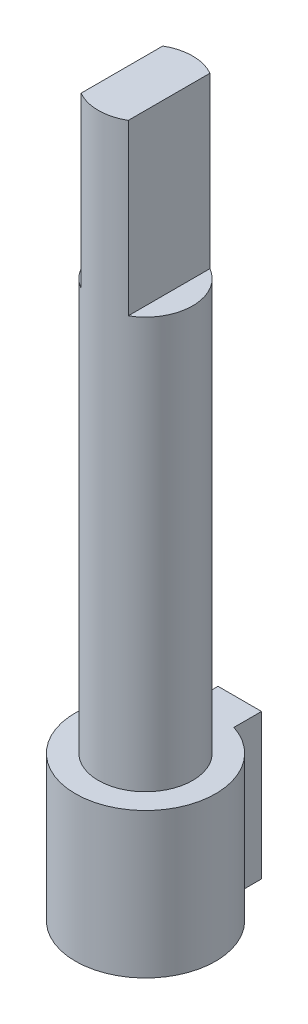
SolidWorks part; units mm, degrees
ref_plane "Front Plane" through (0, 0, 0) normal (0, 0, 1) x (1, 0, 0)
ref_plane "Top Plane" through (0, 0, 0) normal (0, 1, 0) x (1, 0, 0)
ref_plane "Right Plane" through (0, 0, 0) normal (1, 0, 0) x (0, 0, -1)
sketch "Sketch1" plane through (0, 0, 0) normal (0, 1, 0) x (1, 0, 0)
  line L1 (-1, 2.8284) -> (1, 2.8284)
  line L2 (-1, 2.8284) -> (-1, 3.9984)
  line L3 (-1, 3.9984) -> (1, 3.9984)
  line L4 (1, 2.8284) -> (1, 3.9984)
  circle A0 centre (0, 0) radius 3
  point P7 (0, 0)
  point P8 (0, 2.8284)
  dimension "D1" = 6
  dimension "D2" = 1.17
  dimension "D3" = 2
extrude "Boss-Extrude1" add sketch "Sketch1" along normal blind 30 contours L1 A0
sketch "Sketch2" plane through (0, 30, 0) normal (0, 1, 0) x (1, 0, 0)
  circle A0 centre (0, 0) radius 1.95
  circle A1 centre (0, 0) radius 6.1662
  dimension "D1" = 3.9
extrude "Cut-Extrude1" cut sketch "Sketch2" against normal blind 22
sketch "Sketch3" plane through (0, 30, 0) normal (0, 1, 0) x (1, 0, 0)
  line L0 (-0.975, 1.6887) -> (-0.975, -1.6887)
  line L1 (0.975, 1.6887) -> (0.975, -1.6887)
  circle A0 centre (0, 0) radius 1.95 construction
  arc A1 (-0.975, 1.6887) -> (-0.975, -1.6887) centre (0, 0) ccw
  arc A2 (0.975, -1.6887) -> (0.975, 1.6887) centre (0, 0) ccw
  dimension "D1" = 1.95
  dimension "D2" = 0.975
extrude "Cut-Extrude2" cut sketch "Sketch3" against normal blind 7
sketch "Sketch4" plane through (0, 0, 0) normal (0, -1, 0) x (1, 0, 0)
  line L0 (-1, -3.9984) -> (1, -3.9984) construction
  line L1 (1, -2.8284) -> (1, -3.9984) construction
  line L2 (-1, -2.8284) -> (-1, -3.9984) construction
  line L3 (-1, -3.9984) -> (1, -3.9984)
  line L4 (1, -2.8284) -> (1, -3.9984)
  line L5 (-1, -2.8284) -> (-1, -3.9984)
  line L6 (-0.9, -2.7568) -> (-0.9, -3.8984)
  line L7 (-0.9, -3.8984) -> (0.9, -3.8984)
  line L8 (0.9, -2.7568) -> (0.9, -3.8984)
  arc A0 (1, -2.8284) -> (-1, -2.8284) centre (0, 0) ccw construction
  arc A1 (1, -2.8284) -> (-1, -2.8284) centre (0, 0) ccw
  arc A2 (0.9, -2.7568) -> (-0.9, -2.7568) centre (0, 0) ccw
  dimension "D1" = 0.1
extrude "Cut-Extrude3" cut sketch "Sketch4" against normal blind 100
sketch "Sketch5" plane through (0, 8, 0) normal (0, 1, 0) x (1, 0, 0)
  line L0 (-2.7601, 0.89) -> (-1.7089, 4.15)
  line L1 (-1.7089, 4.15) -> (2.1749, 4.15)
  line L2 (2.1749, 4.15) -> (2.4846, 1.4956)
  circle A0 centre (0, 0) radius 1.95
  arc A1 (-2.7601, 0.89) -> (2.4846, 1.4956) centre (0, 0) ccw
extrude "Cut-Extrude4" cut sketch "Sketch5" against normal blind 2
